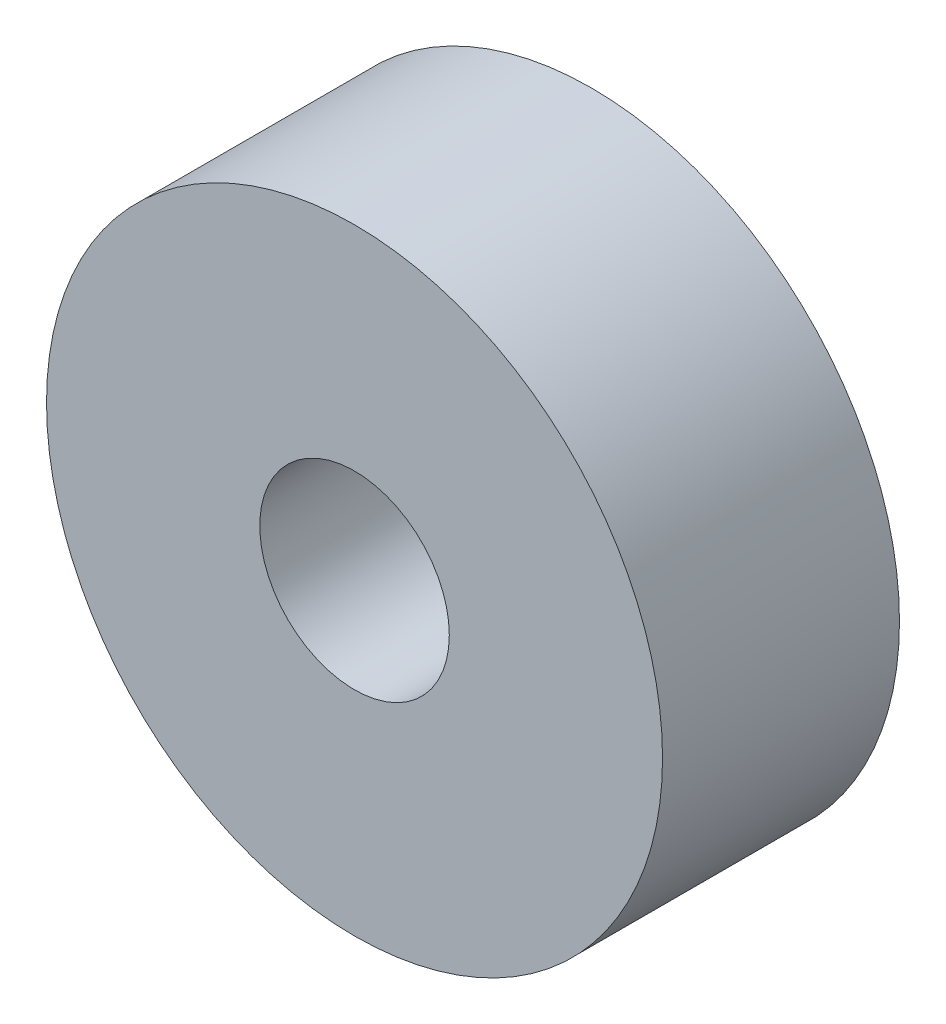
SolidWorks part; units mm, degrees
material "Chrome Stainless Steel"
ref_plane "Front Plane" through (0, 0, 0) normal (0, 0, 1) x (1, 0, 0)
ref_plane "Top Plane" through (0, 0, 0) normal (0, 1, 0) x (1, 0, 0)
ref_plane "Right Plane" through (0, 0, 0) normal (1, 0, 0) x (0, 0, -1)
sketch "Sketch1" plane through (0, 0, 0) normal (0, 0, 1) x (1, 0, 0)
  circle A0 centre (0, 0) radius 2
  circle A1 centre (0, 0) radius 6.5
  dimension "D1" = 4
  dimension "D2" = 13
extrude "Boss-Extrude1" add sketch "Sketch1" along normal mid plane 5
